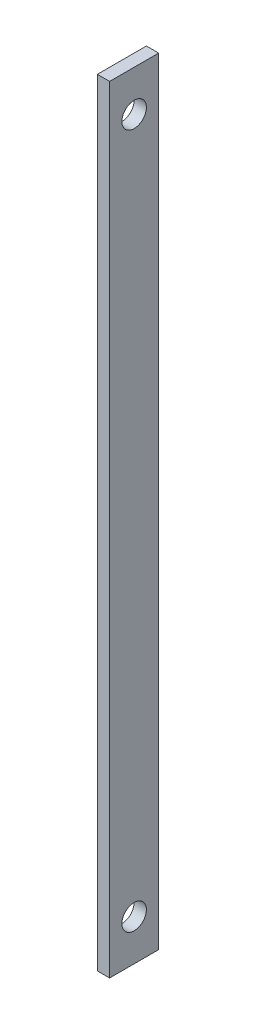
SolidWorks part; units mm, degrees
ref_plane "Front Plane" through (0, 0, 0) normal (0, 0, 1) x (1, 0, 0)
ref_plane "Top Plane" through (0, 0, 0) normal (0, 1, 0) x (1, 0, 0)
ref_plane "Right Plane" through (0, 0, 0) normal (1, 0, 0) x (0, 0, -1)
sketch "Sketch1" plane through (0, 0, 0) normal (1, 0, 0) x (0, 0, -1)
  line L1 (-6, -95) -> (6, -95)
  line L2 (-6, -95) -> (-6, 95)
  line L3 (-6, 95) -> (6, 95)
  line L4 (6, -95) -> (6, 95)
  line L5 (-6, -95) -> (6, 95) construction
  line L6 (-6, 95) -> (6, -95) construction
  point P0 (0, 0)
  dimension "D1" = 190
  dimension "D2" = 12
extrude "Boss-Extrude1" add sketch "Sketch1" along normal blind 3
sketch "Sketch2" plane through (0, 0, 0) normal (-1, 0, 0) x (0, 0, 1)
  line L0 (-6, 95) -> (6, 95) construction
  circle A0 centre (0, 85) radius 3
  circle A1 centre (0, -85) radius 3
  dimension "D1" = 10
  dimension "D3" = 6
  dimension "D2" = 170
extrude "Cut-Extrude1" cut sketch "Sketch2" against normal up to surface (3 mm away) up to face at (3, 0, 0)
